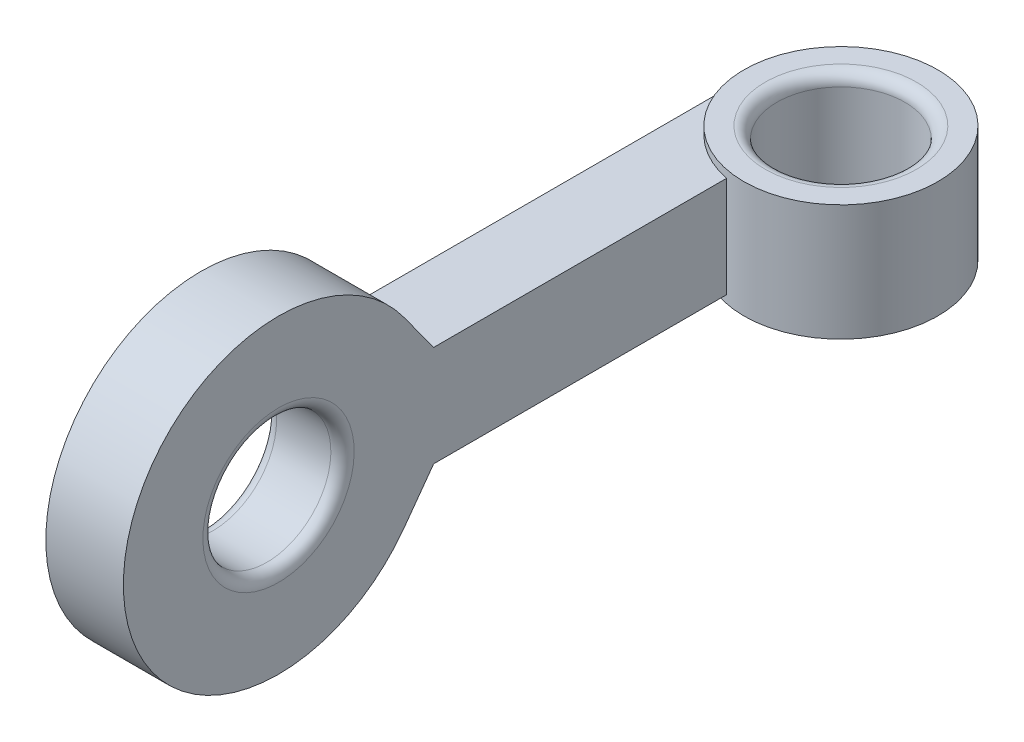
SolidWorks part; units mm, degrees
ref_plane "前视基准面" through (0, 0, 0) normal (0, 0, 1) x (1, 0, 0)
ref_plane "上视基准面" through (0, 0, 0) normal (0, 1, 0) x (1, 0, 0)
ref_plane "右视基准面" through (0, 0, 0) normal (1, 0, 0) x (0, 0, -1)
sketch "草图1" plane through (0, 0, 0) normal (0, 1, 0) x (1, 0, 0)
  circle A0 centre (0, 0) radius 1.65
  circle A1 centre (0, 0) radius 2.5
  dimension "D1" = 3.3
  dimension "D2" = 5
extrude "凸台-拉伸1" add sketch "草图1" along normal blind 3
ref_plane "基准面4" through (0, 0, 10) normal (0, 0, 1) x (1, 0, 0)
sketch "草图2" plane through (0, 0, 10) normal (0, 0, 1) x (1, 0, 0)
  line L0 (0, -0.2944) -> (0, 0.3038) construction
  line L1 (-2.5, 2.8) -> (-0.5, 2.8)
  line L2 (-2.5, 2.8) -> (-2.5, 0.2)
  line L3 (-2.5, 0.2) -> (-0.5, 0.2)
  line L6 (1.65, 3) -> (-1.65, 3) construction
  line L7 (-2.5, 0) -> (2.5, 0) construction
  line L8 (-0.5, 2.8) -> (-0.5, 0.2)
  point P4 (0, 0.0047)
  dimension "D1" = 0.2
  dimension "D2" = 0.2
  dimension "D3" = 2
  dimension "D4" = 0.5
extrude "凸台-拉伸2" add sketch "草图2" against normal up to next
sketch "草图3" plane through (-2.5, 0, 0) normal (-1, 0, 0) x (0, 0, 1)
  line L0 (0, 3) -> (0, 0) construction
  line L1 (1.65, 3) -> (-1.65, 3) construction
  line L2 (0, 1.5) -> (10.5114, 1.5) construction
  line L3 (5, 2.8) -> (10, 2.8) construction
  line L6 (0, 2.8) -> (10, 2.8) construction
  line L7 (4.0412, 0.2) -> (10, 0.2) construction
  line L8 (0, 0.2) -> (10, 0.2) construction
  line L9 (10, 6.8655) -> (10, -2.3372) construction
  line L10 (10, -2.86) -> (10, 2.86) construction
  line L11 (10, 2.8) -> (10, 0.2)
  line L12 (10, 0.2) -> (10.7643, -0.8516)
  line L13 (10, 2.8) -> (10.7643, 3.8516)
  arc A0 (10.7643, -0.8516) -> (10.7643, 3.8516) centre (14, 1.5) ccw
  dimension "D1" = 4
  dimension "D2" = 8
extrude "凸台-拉伸3" add sketch "草图3" against normal up to surface (2 mm away) up to face at (-0.5, 1.5, 6.2247)
sketch "草图4" plane through (-0.5, 0, 0) normal (1, 0, 0) x (0, 0, -1)
  circle A0 centre (-14, 1.5) radius 1.65
  dimension "D1" = 3.3
extrude "切除-拉伸1" cut sketch "草图4" against normal up to next
ref_plane "基准面5" through (0, 1.5, 0) normal (0, 1, 0) x (1, 0, 0)
fillet "圆角1" radius 0.3 1 edges at (-0.5, 3.15, 14)
fillet "圆角2" radius 0.3 1 edges at (0, 3, 1.65)
fillet "圆角3" radius 0.3 1 edges at (0, 0, 1.65)
fillet "圆角4" radius 0.3 1 edges at (-2.5, -0.15, 14)
